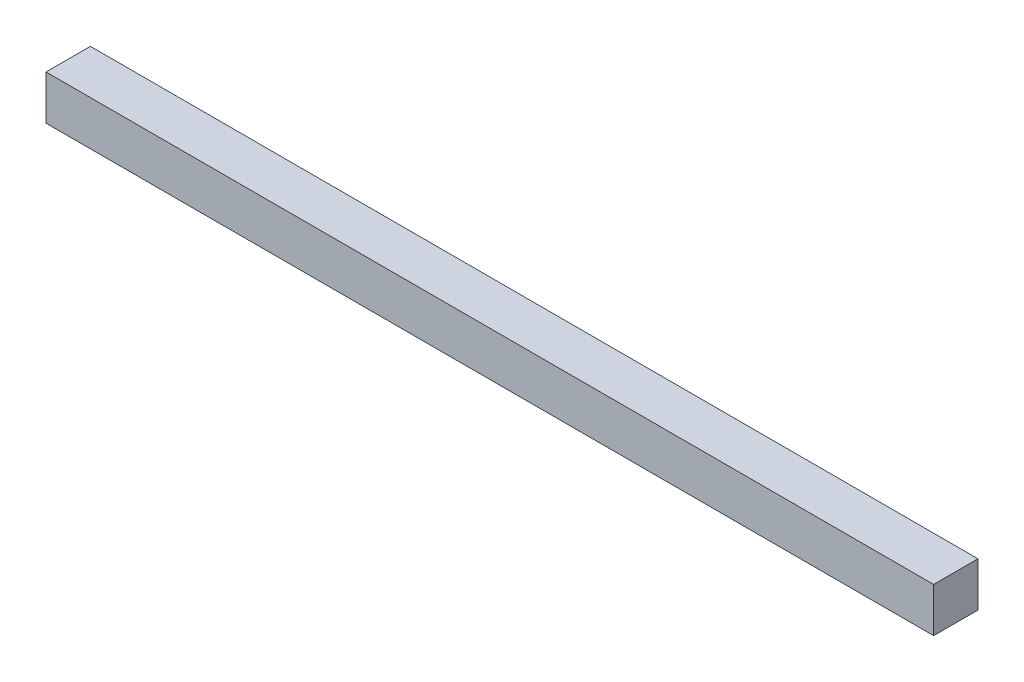
SolidWorks part; units mm, degrees
ref_plane "Plan de face" through (0, 0, 0) normal (0, 0, 1) x (1, 0, 0)
ref_plane "Plan de dessus" through (0, 0, 0) normal (0, 1, 0) x (1, 0, 0)
ref_plane "Plan de droite" through (0, 0, 0) normal (1, 0, 0) x (0, 0, -1)
sketch "Esquisse1" plane through (0, 0, 0) normal (0, 0, 1) x (1, 0, 0)
  line L1 (-5000, -250) -> (5000, -250)
  line L2 (-5000, -250) -> (-5000, 250)
  line L3 (-5000, 250) -> (5000, 250)
  line L4 (5000, -250) -> (5000, 250)
  line L5 (-5000, -250) -> (5000, 250) construction
  line L6 (-5000, 250) -> (5000, -250) construction
  point P0 (0, 0)
  dimension "D1" = 10000
  dimension "D2" = 500
extrude "Boss.-Extru.1" add sketch "Esquisse1" along normal blind 500
